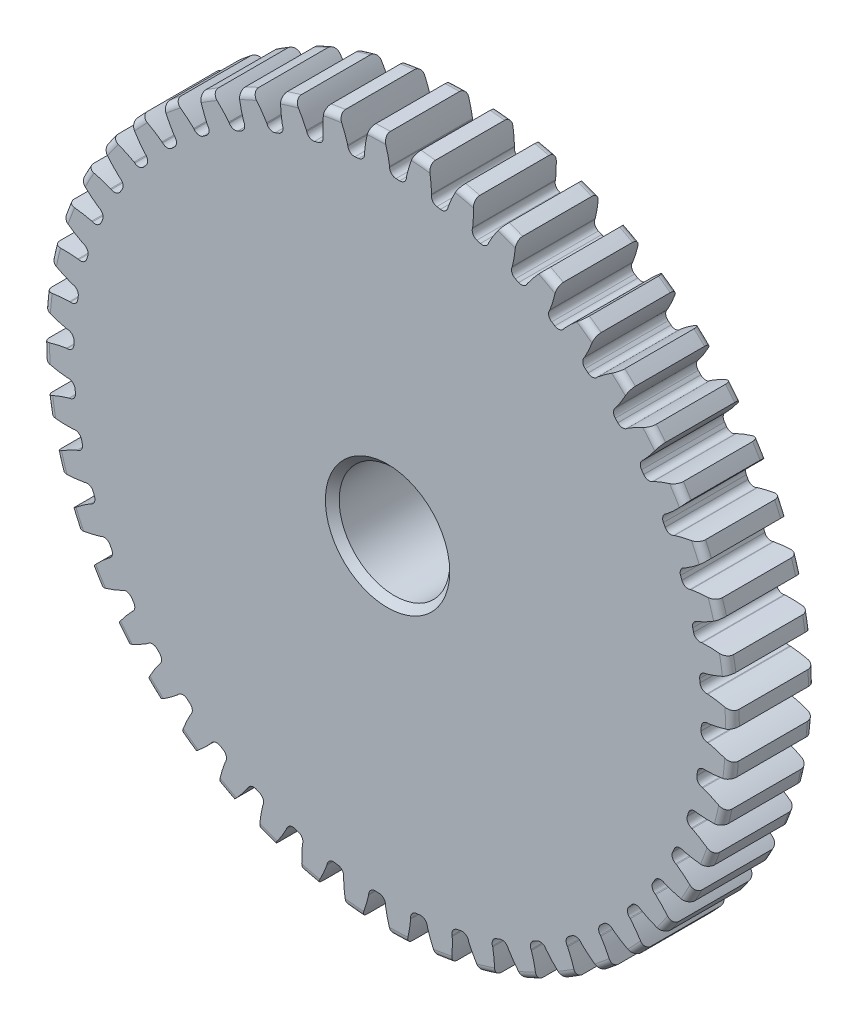
SolidWorks part; units mm, degrees
ref_plane "Front" through (0, 0, 0) normal (0, 0, 1) x (1, 0, 0)
ref_plane "Top" through (0, 0, 0) normal (0, 1, 0) x (1, 0, 0)
ref_plane "Right" through (0, 0, 0) normal (1, 0, 0) x (0, 0, -1)
sketch "Sketch1" plane through (0, 0, 0) normal (0, 0, 1) x (1, 0, 0)
  line L0 (-609.6, 0) -> (609.6, 0) construction
  circle A0 centre (0, 0) radius 19.812
  circle A1 centre (0, 0) radius 19.05 construction
  circle A3 centre (0, 0) radius 18.0261 construction
  dimension "D1" = 1.7859
  dimension "OD" = 39.624
  dimension "Ptich Dia" = 38.1
  dimension "Root Dia" = 36.0521
  dimension "D3" = 0.762
  dimension "Number of Teeth" = 1219.2
extrude "Boss-Extrude1" add sketch "Sketch1" against normal blind 4.7625
sketch "Sketch2" plane through (0, 0, 0) normal (1, 0, 0) x (0, 0, -1)
  line L0 (4.7625, 0) -> (11.1125, 0)
  line L1 (4.7625, 0) -> (4.7625, 7.9375)
  line L2 (4.7625, 7.9375) -> (11.1125, 7.9375)
  line L3 (11.1125, 7.9375) -> (11.1125, 0)
  point P5 (11.1125, -7.9375)
  point P6 (0, -19.812)
  point P7 (4.7625, -19.812)
  point P9 (0, 19.812)
  dimension "Face Wd" = 4.7625
  dimension "B Hub Dia" = 15.875
  dimension "D O'all Lg." = 11.1125
revolve "Revolve1" add sketch "Sketch2" angle 360 about L0
fillet "Fillet2" radius 0.3962 3 edges at (19.812, 0, -4.7625) (19.812, 0, 0) (7.9375, 0, -4.7625)
sketch "Sketch3" plane through (0, 0, 0) normal (0, 0, 1) x (1, 0, 0)
  line L0 (0, 0) -> (0, 19.812) construction
  line L1 (-4.6178, 17.8558) -> (0, 19.05)
  line L2 (-9.5921, 19.05) -> (9.5921, 19.05) construction
  line L3 (-9.2865, 16.6483) -> (9.2865, 21.4517) construction
  line L4 (-4.6178, 17.8558) -> (0, 0) construction
  line L5 (-11.7785, 14.1922) -> (0, 0) construction
  line L6 (-11.7785, 14.1922) -> (-1.888, 22.4005) construction
  line L7 (-3.22, 18.16) -> (0, 0) construction
  line L8 (-3.22, 18.16) -> (0.0676, 18.7429) construction
  arc A0 (-4.6178, 17.8558) -> (-11.7785, 14.1922) centre (0, 0) ccw
  circle A1 centre (0, 0) radius 19.05 construction
  circle A2 centre (0, 0) radius 18.4432 construction
  arc A3 (-4.6178, 17.8558) -> (-3.22, 18.16) centre (0, 0) cw
  circle A4 centre (0, 0) radius 19.812 construction
  point P6 (0, 19.05)
  dimension "D1" = 4.7697
  dimension "Pressure Angle" = 14.5
  dimension "D2" = 8.1086
  dimension "D3" = 12.8529
  dimension "D4" = 1.4309
  dimension "D5" = 3.3388
sketch "Sketch4" plane through (0, 0, 0) normal (0, 0, 1) x (1, 0, 0)
  line L0 (0, 0) -> (0.623, 19.0296) construction
  line L1 (0.1199, 18.4428) -> (0.1199, 18.0257)
  line L2 (0, 19.05) -> (1.2459, 19.0092) construction
  line L3 (1.0866, 18.4112) -> (1.0593, 17.9949)
  line L4 (0.1199, 18.0257) -> (0, 0) construction
  line L5 (0, 0) -> (0, 19.812) construction
  line L6 (-11.7785, 14.1922) -> (-1.888, 22.4005) construction
  line L7 (-11.7785, 14.1922) -> (-1.888, 22.4005) construction
  arc A0 (1.0593, 17.9949) -> (0.1199, 18.0257) centre (0, 0) ccw
  arc A1 (0, 19.05) -> (1.2459, 19.0092) centre (0, 0) cw construction
  circle A2 centre (0, 0) radius 19.05 construction
  circle A3 centre (0, 0) radius 18.4432 construction
  circle A4 centre (0, 0) radius 18.0261 construction
  arc A5 (3.3491, 22.2291) -> (-1.888, 22.4005) centre (0, 0) ccw
  spline S0 degree 2 poles (-1.888, 22.4005) (-0.2168, 20.6516) (0.1199, 18.4428) knots 0 0 0 1 1 1
  spline S1 degree 2 poles (3.3491, 22.2291) (1.5671, 20.5932) (1.0866, 18.4112) knots 0 0 0 1 1 1
  dimension "D1" = 1.2468
extrude "Cut-Extrude1" cut sketch "Sketch4" against normal through all
fillet "Fillet1" radius 0.374 2 edges at (1.0593, 17.9949, -2.3813) (0.1199, 18.0257, -2.3813)
pattern_circular "CirPattern1" count 48 over 360 about axis through (0, 0, -4.7625) along (0, 0, 1) of "Cut-Extrude1", "Fillet1"
sketch "Sketch5" plane through (0, 0, 0) normal (0, 0, 1) x (1, 0, 0)
  circle A0 centre (0, 0) radius 3.175
  circle A1 centre (0, 0) radius 1.5875 construction
  dimension "Bore Min" = 6.35
  dimension "Bore Max" = 3.175
extrude "Cut-Extrude2" cut sketch "Sketch5" against normal through all
chamfer "Chamfer1" distance 0.3969 angle 45 3 edges at (7.9375, 0, -11.1125) (3.175, 0, 0) (3.175, 0, -11.1125)
sketch "Pitch Dia" plane through (0, 0, 0) normal (0, 0, 1) x (1, 0, 0)
  circle A0 centre (0, 0) radius 19.05 construction
  circle A1 centre (0, 0) radius 19.05 construction
equation "\"D1@Boss-Extrude1\" = \"Face Wd@Sketch2\""
equation "\"D2@Sketch3\" = \"D1@Sketch3\"*1.7"
equation "\"D3@Sketch3\" = \"D1@Sketch3\"+\"D2@Sketch3\"-.001"
equation "\"D4@Sketch3\" = \"D1@Sketch3\"*.3"
equation "\"D5@Sketch3\" = \"D1@Sketch3\"-\"D4@Sketch3\""
equation "\"D1@Sketch4\" = 1.5708/(\"Number of Teeth@Sketch1\"/\"Ptich Dia@Sketch1\")"
equation "\"D1@Chamfer1\" = \"B Hub Dia@Sketch2\"*.025"
equation "\"D1@CirPattern1\" = \"Number of Teeth@Sketch1\""
equation "\"D1@Fillet1\" = \"D1@Sketch4\"*.3"
equation "\"D1@Fillet2\" = \"OD@Sketch1\"*.01"
equation "\"D1@Sketch1\" = 2.250/(\"Number of Teeth@Sketch1\"/\"Ptich Dia@Sketch1\")"
